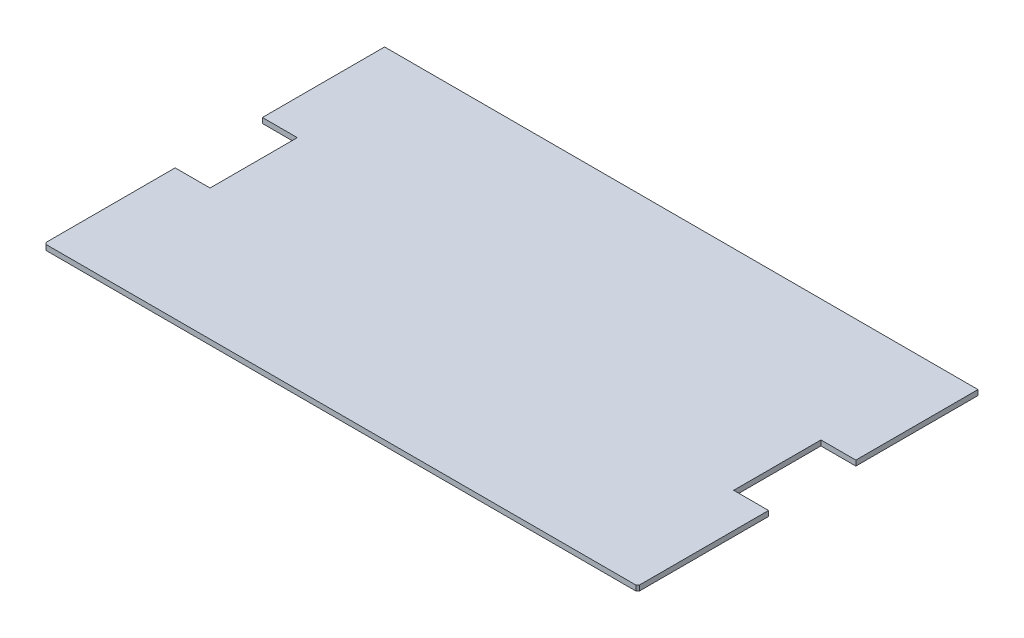
SolidWorks part; units mm, degrees
ref_plane "Front Plane" through (0, 0, 0) normal (0, 0, 1) x (1, 0, 0)
ref_plane "Top Plane" through (0, 0, 0) normal (0, 1, 0) x (1, 0, 0)
ref_plane "Right Plane" through (0, 0, 0) normal (1, 0, 0) x (0, 0, -1)
sketch "Sketch1" plane through (0, 0, 0) normal (0, 1, 0) x (1, 0, 0)
  line L0 (-170, -97.5) -> (-170, -22.5)
  line L1 (-170, -22.5) -> (-150, -22.5)
  line L2 (-150, -22.5) -> (-150, 27.5)
  line L3 (-150, 27.5) -> (-170, 27.5)
  line L4 (-170, -97.5) -> (170, -97.5)
  line L5 (170, -97.5) -> (170, -22.5)
  line L6 (170, -22.5) -> (150, -22.5)
  line L7 (150, -22.5) -> (150, 27.5)
  line L8 (150, 27.5) -> (170, 27.5)
  line L9 (-170, 27.5) -> (-170, 97.5)
  line L10 (-170, 97.5) -> (170, 97.5)
  line L11 (170, 97.5) -> (170, 27.5)
extrude "Boss-Extrude1" add sketch "Sketch1" along normal blind 3
chamfer "Chamfer1" distance 1 angle 45 2 edges at (-170, 1.5, 97.5) (170, 1.5, 97.5)
